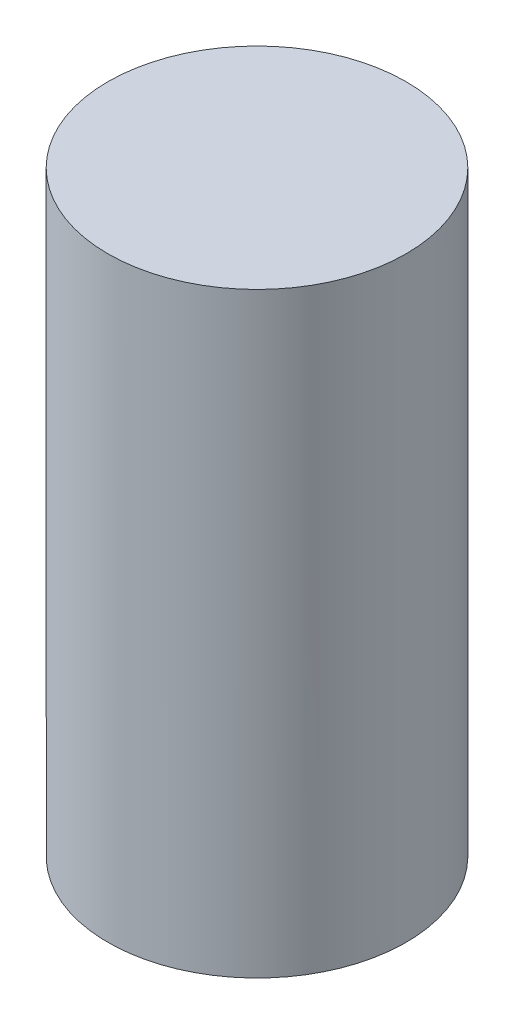
SolidWorks part; units mm, degrees
material "AISI 4340 Steel, normalized"
ref_plane "Front Plane" through (0, 0, 0) normal (0, 0, 1) x (1, 0, 0)
ref_plane "Top Plane" through (0, 0, 0) normal (0, 1, 0) x (1, 0, 0)
ref_plane "Right Plane" through (0, 0, 0) normal (1, 0, 0) x (0, 0, -1)
sketch "Sketch1" plane through (0, 0, 0) normal (0, 1, 0) x (1, 0, 0)
  circle A0 centre (0, 0) radius 0.375
  dimension "D1" = 0.75
extrude "Boss-Extrude1" add sketch "Sketch1" along normal mid plane 0.25
sketch "Sketch2" plane through (0, 0.125, 0) normal (0, 1, 0) x (1, 0, 0)
  circle A1 centre (0, 0) radius 0.375
  circle A2 centre (0, 0) radius 0.375
  dimension "D1" = 0
extrude "Boss-Extrude2" add sketch "Sketch2" along normal blind 0.625
sketch "Sketch3" plane through (0, -0.125, 0) normal (0, -1, 0) x (1, 0, 0)
  circle A1 centre (0, 0) radius 0.375
  circle A2 centre (0, 0) radius 0.375
  dimension "D1" = 0
extrude "Boss-Extrude3" add sketch "Sketch3" along normal blind 0.625
